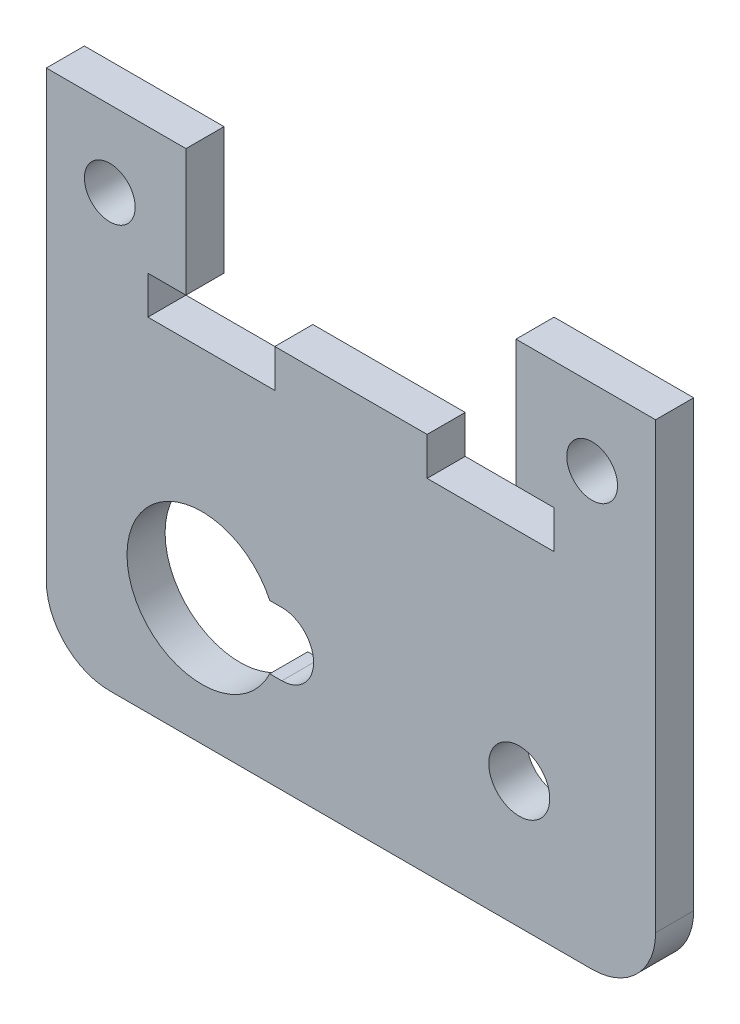
SolidWorks part; units mm, degrees
ref_plane "Alzado" through (0, 0, 0) normal (0, 0, 1) x (1, 0, 0)
ref_plane "Planta" through (0, 0, 0) normal (0, 1, 0) x (1, 0, 0)
ref_plane "Vista lateral" through (0, 0, 0) normal (1, 0, 0) x (0, 0, -1)
sketch "Model" plane through (0, 0, 0) normal (0, 0, 1) x (1, 0, 0)
  line L0 (60.128, 43.8101) -> (60.128, 26.9884)
  line L1 (108.128, 43.8101) -> (97.128, 43.8101)
  line L2 (71.128, 43.8101) -> (60.128, 43.8101)
  line L3 (108.128, 8.8101) -> (108.128, 43.8101)
  line L4 (103.128, 3.8101) -> (65.128, 3.8101)
  line L5 (78.6835, 11.278) -> (77.7263, 11.278)
  line L6 (78.6835, 16.278) -> (77.7289, 16.278)
  line L7 (90.128, 30.8101) -> (100.128, 30.8101)
  line L8 (97.128, 33.8101) -> (100.128, 33.8101)
  line L9 (78.128, 30.8101) -> (68.128, 30.8101)
  line L10 (71.128, 33.8101) -> (68.128, 33.8101)
  line L11 (100.128, 30.8101) -> (100.128, 33.8101)
  line L12 (90.128, 30.8101) -> (90.128, 33.8101)
  line L13 (78.128, 30.8101) -> (78.128, 33.8101)
  line L14 (60.128, 26.9884) -> (60.128, 8.8101)
  line L15 (97.128, 43.8101) -> (97.128, 33.8101)
  line L16 (71.128, 33.8101) -> (71.128, 43.8101)
  line L17 (78.128, 33.8101) -> (90.128, 33.8101)
  line L18 (68.128, 33.8101) -> (68.128, 30.8101)
  circle A0 centre (97.3861, 13.789) radius 2.4
  circle A1 centre (65.128, 37.8101) radius 2
  circle A2 centre (103.128, 37.8101) radius 2
  arc A3 (78.6835, 11.278) -> (78.6835, 16.278) centre (78.6835, 13.778) ccw
  arc A4 (77.7289, 16.278) -> (77.7263, 11.278) centre (72.3835, 13.7808) ccw
  arc A5 (103.128, 3.8101) -> (108.128, 8.8101) centre (103.128, 8.8101) ccw
  arc A6 (60.128, 8.8101) -> (65.128, 3.8101) centre (65.128, 8.8101) ccw
extrude "Saliente-Extruir1" add sketch "Model" along normal blind 3
